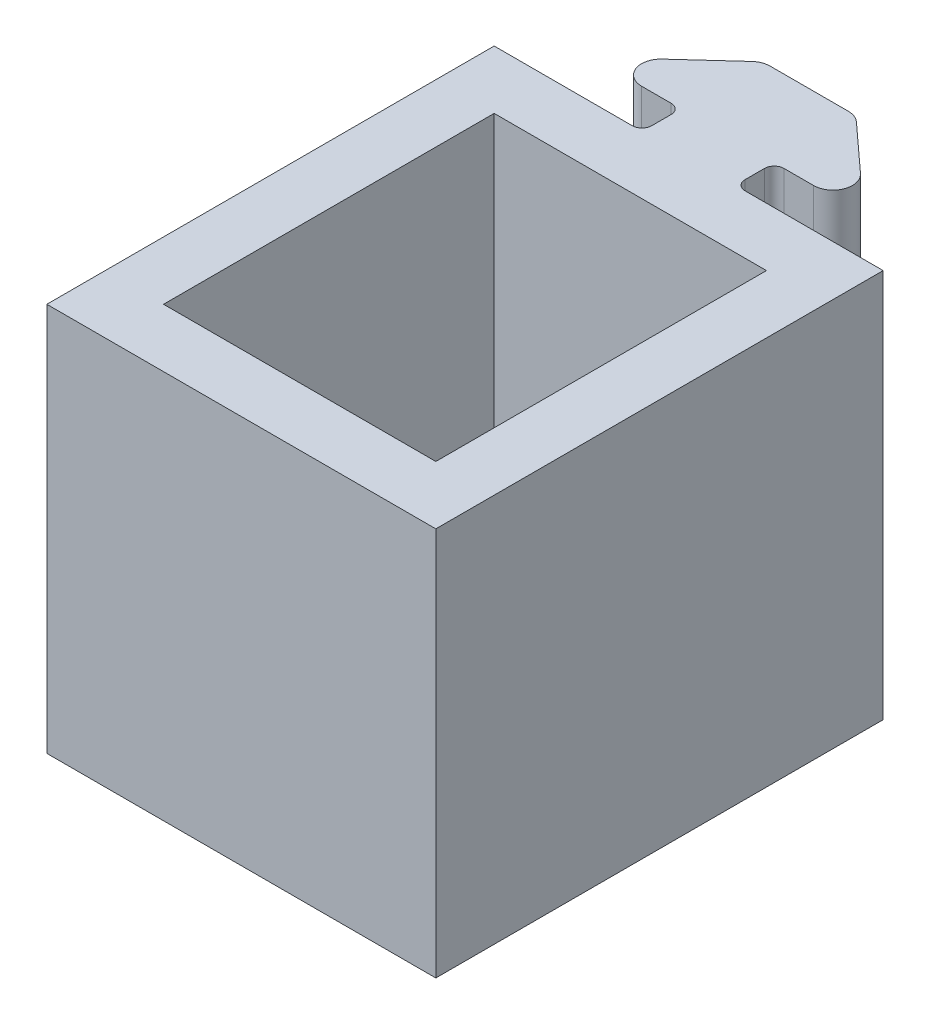
SolidWorks part; units mm, degrees
ref_plane "Front Plane" through (0, 0, 0) normal (0, 0, 1) x (1, 0, 0)
ref_plane "Top Plane" through (0, 0, 0) normal (0, 1, 0) x (1, 0, 0)
ref_plane "Right Plane" through (0, 0, 0) normal (1, 0, 0) x (0, 0, -1)
sketch "Sketch1" plane through (0, 0, 0) normal (0, 1, 0) x (1, 0, 0)
  line L0 (0, 0) -> (0, 4.5818) construction
  line L1 (-2.4, 4.5818) -> (2.4, 4.5818)
  line L2 (2.4, 4.5818) -> (7, 0.3818)
  line L3 (7, 0.3818) -> (2.4, 0.3818)
  line L4 (2.4, 0.3818) -> (2.4, -1.6182)
  line L5 (2.4, -1.6182) -> (10, -1.6182)
  line L6 (10, -1.6182) -> (10, -4.6182)
  line L7 (10, -4.6182) -> (-10, -4.6182)
  line L8 (-10, -1.6182) -> (-10, -4.6182)
  line L9 (-2.4, -1.6182) -> (-10, -1.6182)
  line L10 (-2.4, 0.3818) -> (-2.4, -1.6182)
  line L11 (-7, 0.3818) -> (-2.4, 0.3818)
  line L12 (-2.4, 4.5818) -> (-7, 0.3818)
  point P11 (0, -4.6182)
  dimension "D1" = 2.4
  dimension "D2" = 6.2
  dimension "D3" = 7
  dimension "D4" = 2
  dimension "D5" = 10
  dimension "D6" = 4.8
  dimension "D7" = 3
extrude "Boss-Extrude1" add sketch "Sketch1" along normal blind 20
fillet "Fillet1" radius 1 4 edges at (2.4, 10, -4.5818) (-2.4, 10, -4.5818) (-7, 10, -0.3818) (7, 10, -0.3818)
fillet "Fillet2" radius 0.5 4 edges at (2.4, 10, 1.6182) (2.4, 10, -0.3818) (-2.4, 10, 1.6182) (-2.4, 10, -0.3818)
sketch "Sketch2" plane through (0, 20, 0) normal (0, 1, 0) x (1, 0, 0)
  line L0 (10, -4.6182) -> (10, -1.6182) construction
  line L1 (-10, -4.6182) -> (10, -4.6182)
  line L2 (-10, -4.6182) -> (-10, -24.6182)
  line L3 (-10, -24.6182) -> (10, -24.6182)
  line L4 (10, -4.6182) -> (10, -24.6182)
  line L5 (-7, -4.6182) -> (7, -4.6182)
  line L6 (-7, -4.6182) -> (-7, -21.6182)
  line L7 (-7, -21.6182) -> (7, -21.6182)
  line L8 (7, -4.6182) -> (7, -21.6182)
  line L9 (-2.9, -1.6182) -> (-10, -1.6182) construction
  line M19 (-10, -4.6182) -> (10, -4.6182)
  dimension "D1" = 3
  dimension "D2" = 3
  dimension "D3" = 3
  dimension "D4" = 23
extrude "Boss-Extrude2" add sketch "Sketch2" against normal blind 20 contours L8 L7 L6 L2 L3 L4 M19
